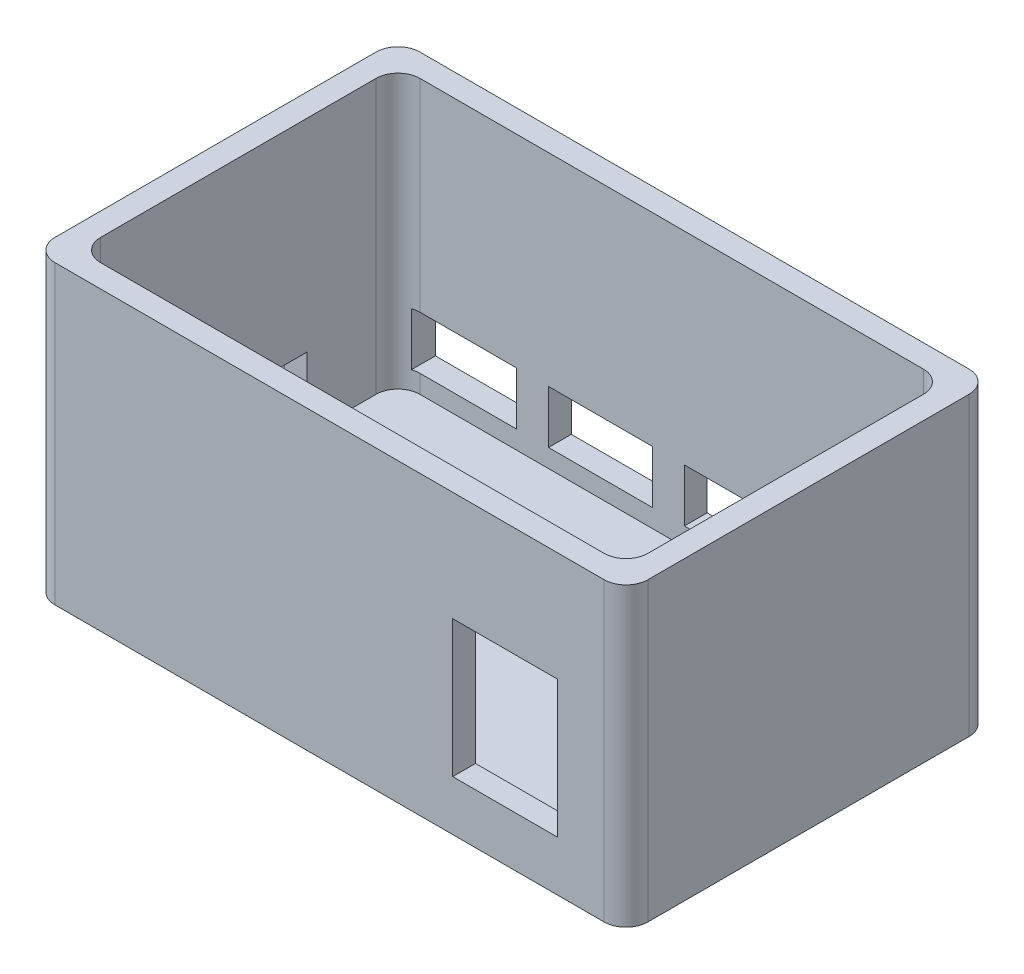
SolidWorks part; units mm, degrees
ref_plane "Front Plane" through (0, 0, 0) normal (0, 0, 1) x (1, 0, 0)
ref_plane "Top Plane" through (0, 0, 0) normal (0, 1, 0) x (1, 0, 0)
ref_plane "Right Plane" through (0, 0, 0) normal (1, 0, 0) x (0, 0, -1)
sketch "Sketch1" plane through (0, 0, 0) normal (0, 1, 0) x (1, 0, 0)
  line L1 (0, 0) -> (76.2, 0)
  line L2 (0, 0) -> (0, -44.45)
  line L3 (0, -44.45) -> (76.2, -44.45)
  line L4 (76.2, 0) -> (76.2, -44.45)
  dimension "D1" = 76.2
  dimension "D2" = 44.45
extrude "Boss-Extrude1" add sketch "Sketch1" along normal blind 38.1
shell "Shell1" thickness 3.175
sketch "Sketch3" plane through (-3.175, 0, 0) normal (-1, 0, 0) x (0, 0, 1)
  line L0 (0, 38.1) -> (0, 0) construction
  line L1 (12.7, 9.906) -> (38.1, 9.906)
  line L2 (12.7, 9.906) -> (12.7, 2.54)
  line L3 (12.7, 2.54) -> (38.1, 2.54)
  line L4 (38.1, 9.906) -> (38.1, 2.54)
  line L5 (0, 0) -> (44.45, 0) construction
  dimension "D1" = 25.4
  dimension "D2" = 7.366
  dimension "D3" = 12.7
  dimension "D4" = 2.54
extrude "Cut-Extrude2" cut sketch "Sketch3" against normal blind 12.7
fillet "Fillet1" radius 3.048 8 edges at (0, 19.05, 0) (-3.175, 17.4625, -3.175) (0, 19.05, 44.45) (-3.175, 17.4625, 47.625) (79.375, 17.4625, 47.625) (76.2, 19.05, 44.45) (76.2, 19.05, 0) (79.375, 17.4625, -3.175)
sketch "Sketch5" plane through (0, 0, -3.175) normal (0, 0, -1) x (-1, 0, 0)
  line L0 (0, 0) -> (0, 38.1) construction
  line L1 (-54.356, 9.906) -> (-39.878, 9.906)
  line L2 (-54.356, 9.906) -> (-54.356, 2.54)
  line L3 (-54.356, 2.54) -> (-39.878, 2.54)
  line L4 (-39.878, 9.906) -> (-39.878, 2.54)
  line L5 (-35.433, 9.906) -> (-20.955, 9.906)
  line L6 (-35.433, 9.906) -> (-35.433, 2.54)
  line L7 (-35.433, 2.54) -> (-20.955, 2.54)
  line L8 (-20.955, 9.906) -> (-20.955, 2.54)
  line L9 (-16.51, 9.906) -> (-2.032, 9.906)
  line L10 (-16.51, 9.906) -> (-16.51, 2.54)
  line L11 (-16.51, 2.54) -> (-2.032, 2.54)
  line L12 (-2.032, 9.906) -> (-2.032, 2.54)
  line L13 (-73.152, 0) -> (-3.048, 0) construction
  dimension "D1" = 4.445
  dimension "D2" = 4.445
  dimension "D3" = 7.366
  dimension "D4" = 14.478
  dimension "D5" = 2.032
  dimension "D6" = 2.54
sketch "Sketch6" plane through (0, 0, 47.625) normal (0, 0, 1) x (1, 0, 0)
  line L0 (3.048, 0) -> (73.152, 0) construction
  line L1 (55.245, 22.86) -> (69.85, 22.86)
  line L2 (55.245, 22.86) -> (55.245, 3.81)
  line L3 (55.245, 3.81) -> (69.85, 3.81)
  line L4 (69.85, 22.86) -> (69.85, 3.81)
  line L7 (76.2, 0) -> (76.2, 38.1) construction
  dimension "D1" = 14.605
  dimension "D2" = 19.05
  dimension "D3" = 3.81
  dimension "D4" = 6.35
extrude "Cut-Extrude4" cut sketch "Sketch6" against normal blind 12.7
extrude "Cut-Extrude5" cut sketch "Sketch5" against normal blind 12.7
